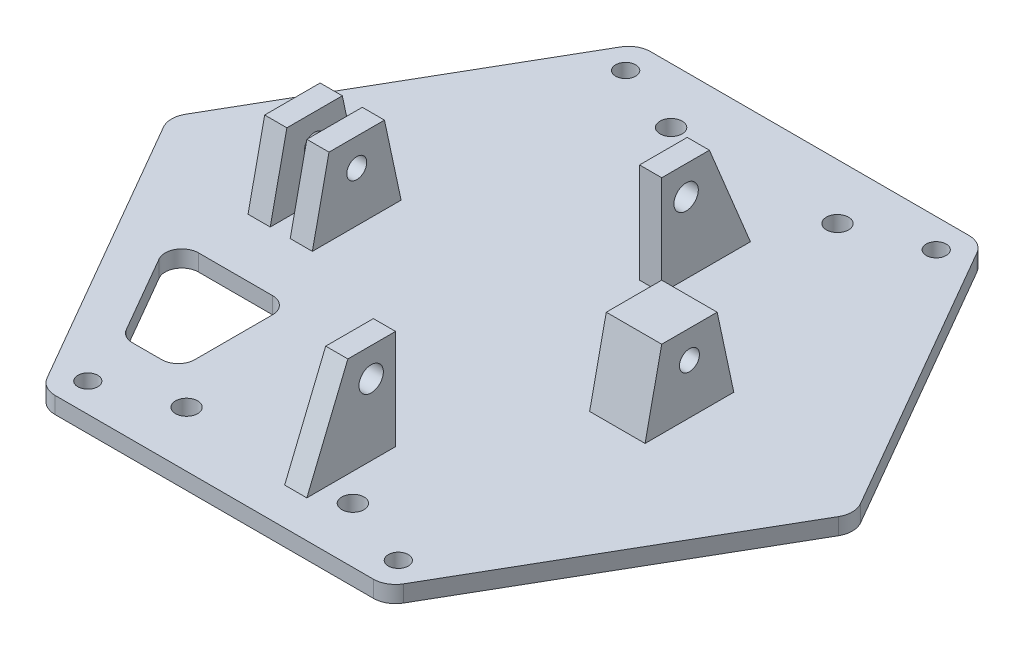
SolidWorks part; units mm, degrees
ref_plane "前视基准面" through (0, 0, 0) normal (0, 0, 1) x (1, 0, 0)
ref_plane "上视基准面" through (0, 0, 0) normal (0, 1, 0) x (1, 0, 0)
ref_plane "右视基准面" through (0, 0, 0) normal (1, 0, 0) x (0, 0, -1)
sketch "草图1" plane through (0, 0, 0) normal (0, 1, 0) x (1, 0, 0)
  line L0 (0, 0) -> (31.5824, 0) construction
  line L1 (15.5, 26.8468) -> (-15.5, 26.8468)
  line L2 (-15.5, 26.8468) -> (-31, 0)
  line L3 (-31, 0) -> (-15.5, -26.8468)
  line L4 (-15.5, -26.8468) -> (15.5, -26.8468)
  line L5 (15.5, -26.8468) -> (31, 0)
  line L6 (31, 0) -> (15.5, 26.8468)
  line L7 (0, 42.7275) -> (0, 0) construction
  circle A0 centre (0, 0) radius 26.8468 construction
  circle A1 centre (24.25, 13.25) radius 1 construction
  circle A2 centre (24.25, -13.25) radius 1 construction
  circle A3 centre (-24.25, -13.25) radius 1 construction
  circle A4 centre (-24.25, 13.25) radius 1 construction
  dimension "D2" = 2
  dimension "D1" = 31
  dimension "D3" = 48.5
  dimension "D4" = 26.5
extrude "凸台-拉伸1" add sketch "草图1" along normal blind 1.5
ref_plane "基准面1" through (16, 0, 0) normal (1, 0, 0) x (0, 0, -1)
ref_plane "基准面2" through (17.8, 0, 0) normal (1, 0, 0) x (0, 0, -1)
sketch "草图3" plane through (16, 0, 0) normal (1, 0, 0) x (0, 0, -1)
  line L0 (-4, 1.5) -> (-2.5, 8.5)
  line L2 (-2.5, 8.5) -> (2.5, 8.5)
  line L3 (2.5, 8.5) -> (4, 1.5)
  line L4 (4, 1.5) -> (-4, 1.5)
  line L5 (0, 6) -> (0, 1.5) construction
  line L6 (0, 0) -> (0, 20.5527) construction
  line L11 (0, 1.5) -> (26.8468, 1.5) construction
  circle A0 centre (0, 6) radius 0.9
  dimension "D1" = 1.8
  dimension "D2" = 8
  dimension "D3" = 5
  dimension "D4" = 4.5
  dimension "D5" = 7
extrude "凸台-拉伸2" add sketch "草图3" against normal blind 2
sketch "草图4" plane through (17.8, 0, 0) normal (1, 0, 0) x (0, 0, -1)
  line L4 (-4, 1.5) -> (4, 1.5)
  line L5 (4, 1.5) -> (2.5, 8.5)
  line L6 (2.5, 8.5) -> (-2.5, 8.5)
  line L7 (-2.5, 8.5) -> (-4, 1.5)
  line L8 (-4, 1.5) -> (4, 1.5)
  line L9 (4, 1.5) -> (2.5, 8.5)
  line L10 (2.5, 8.5) -> (-2.5, 8.5)
  line L11 (-2.5, 8.5) -> (-4, 1.5)
  circle A1 centre (0, 6) radius 0.9 construction
  circle A3 centre (0, 6) radius 0.9
  dimension "D1" = 0
extrude "凸台-拉伸3" add sketch "草图4" along normal blind 2
mirror "镜向3" about plane through (0, 0, 0) normal (1, 0, 0) of "凸台-拉伸3", "凸台-拉伸2"
ref_plane "基准面3" through (5, 0, 0) normal (1, 0, 0) x (0, 0, -1)
sketch "草图5" plane through (5, 0, 0) normal (1, 0, 0) x (0, 0, -1)
  line L1 (-19.8, 10.5) -> (-15.5, 10.5)
  line L2 (-19.8, 10.5) -> (-23.5, 1.5)
  line L3 (-23.5, 1.5) -> (-15.5, 1.5)
  line L4 (-15.5, 10.5) -> (-15.5, 1.5)
  line L5 (-26.8468, 1.5) -> (0, 1.5) construction
  line L6 (-3.5, 1.5) -> (-3.5, 13.649) construction
  line L7 (8.5, 10.5) -> (8.5, 1.5)
  line L8 (16.5, 1.5) -> (8.5, 1.5)
  line L9 (12.8, 10.5) -> (16.5, 1.5)
  line L10 (12.8, 10.5) -> (8.5, 10.5)
  circle A0 centre (-17.7, 7.9) radius 1.1
  circle A1 centre (10.7, 7.9) radius 1.1
  dimension "D1" = 2.2
  dimension "D2" = 6.4
  dimension "D3" = 9
  dimension "D4" = 2.2
  dimension "D5" = 4.3
  dimension "D6" = 8
  dimension "D7" = 24
  dimension "D8" = 3.5
extrude "凸台-拉伸4" add sketch "草图5" against normal blind 2
fillet "圆角1" radius 2 6 edges at (15.5, 0.75, -26.8468) (-15.5, 0.75, -26.8468) (15.5, 0.75, 26.8468) (-15.5, 0.75, 26.8468) (31, 0.75, 0) (-31, 0.75, 0)
sketch "草图6" plane through (0, 0, 0) normal (0, -1, 0) x (1, 0, 0)
  line L0 (0, 29.6949) -> (0, 0) construction
  line L1 (0, 0) -> (-41.4724, 0) construction
  line L2 (-14.9785, 19.25) -> (-12.3446, 19.25)
  line L3 (-10.8446, 17.75) -> (-10.8446, 10.75)
  line L4 (-12.3446, 9.25) -> (-19.02, 9.25)
  line L5 (-20.319, 11.5) -> (-16.2776, 18.5)
  line L8 (-30.4226, 1) -> (-16.0774, 25.8468) construction
  circle A0 centre (-14, 24.25) radius 0.9
  circle A1 centre (14, 24.25) radius 0.9
  circle A2 centre (14, -24.25) radius 0.9
  circle A3 centre (-14, -24.25) radius 0.9
  arc A4 (-10.8446, 10.75) -> (-12.3446, 9.25) centre (-12.3446, 10.75) cw
  arc A5 (-12.3446, 19.25) -> (-10.8446, 17.75) centre (-12.3446, 17.75) cw
  arc A6 (-14.9785, 19.25) -> (-16.2776, 18.5) centre (-14.9785, 17.75) ccw
  arc A7 (-19.02, 9.25) -> (-20.319, 11.5) centre (-19.02, 10.75) cw
  point P22 (-10.8446, 9.25)
  point P25 (-10.8446, 19.25)
  point P28 (-15.8446, 19.25)
  dimension "D1" = 1.8
  dimension "D7" = 5
  dimension "D8" = 1.5
  dimension "D2" = 28
  dimension "D3" = 48.5
  dimension "D4" = 5
  dimension "D5" = 10
  dimension "D6" = 3.5
extrude "切除-拉伸1" cut sketch "草图6" against normal blind 10
sketch "草图7" plane through (0, 0, 0) normal (0, -1, 0) x (1, 0, 0)
  line L0 (0, 0) -> (0, -32.3207) construction
  line L1 (14.3453, -26.8468) -> (-14.3453, -26.8468) construction
  line L2 (0, 0) -> (-40.5194, 0) construction
  circle A0 centre (-7.5, -21.8468) radius 1
  circle A1 centre (7.5, -21.8468) radius 1
  circle A2 centre (7.5, 21.8468) radius 1
  circle A3 centre (-7.5, 21.8468) radius 1
  dimension "D1" = 2
  dimension "D2" = 15
  dimension "D3" = 5
extrude "切除-拉伸2" cut sketch "草图7" against normal blind 10
sketch "草图8" plane through (14, 0, 0) normal (-1, 0, 0) x (0, 0, 1)
  line L4 (-4, 1.5) -> (4, 1.5)
  line L5 (4, 1.5) -> (2.5, 8.5)
  line L6 (2.5, 8.5) -> (-2.5, 8.5)
  line L7 (-2.5, 8.5) -> (-4, 1.5)
  line L8 (-4, 1.5) -> (4, 1.5)
  line L9 (4, 1.5) -> (2.5, 8.5)
  line L10 (2.5, 8.5) -> (-2.5, 8.5)
  line L11 (-2.5, 8.5) -> (-4, 1.5)
  circle A0 centre (0, 6) radius 0.9 construction
  circle A1 centre (0, 6) radius 0.9
  dimension "D1" = 0
extrude "凸台-拉伸5" add sketch "草图8" along normal blind 3
sketch "草图9" plane through (19.8, 0, 0) normal (1, 0, 0) x (0, 0, -1)
  line L4 (-2.5, 8.5) -> (-4, 1.5)
  line L5 (-4, 1.5) -> (4, 1.5)
  line L6 (4, 1.5) -> (2.5, 8.5)
  line L7 (2.5, 8.5) -> (-2.5, 8.5)
  line L8 (-2.5, 8.5) -> (-4, 1.5)
  line L9 (-4, 1.5) -> (4, 1.5)
  line L10 (4, 1.5) -> (2.5, 8.5)
  line L11 (2.5, 8.5) -> (-2.5, 8.5)
  dimension "D1" = 0
extrude "切除-拉伸3" cut sketch "草图9" against normal blind 3
